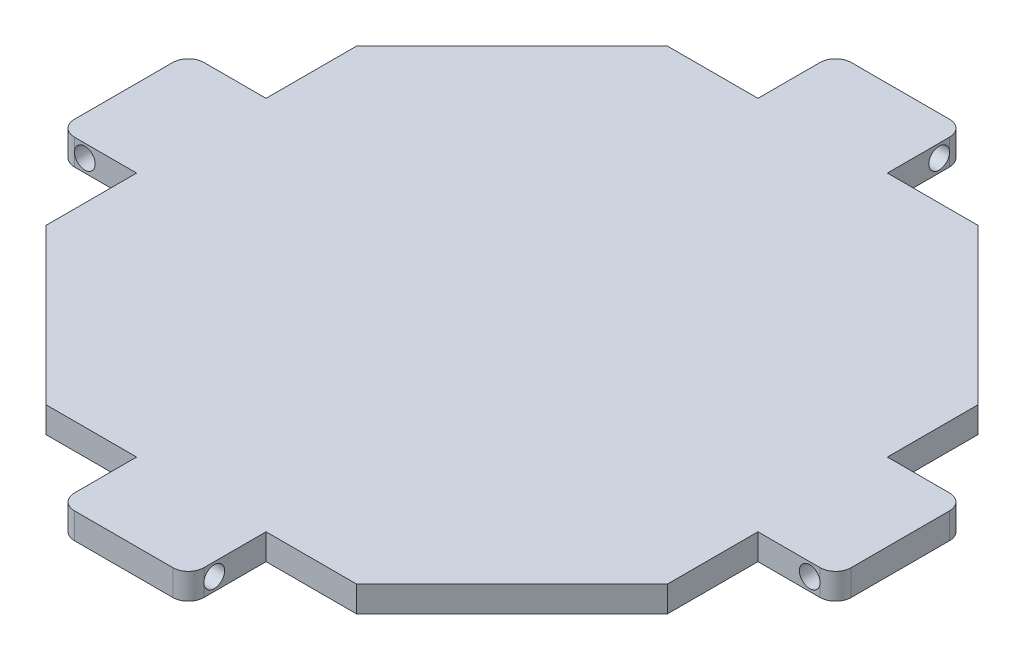
SolidWorks part; units mm, degrees
material "6061 합금"
ref_plane "정면" through (0, 0, 0) normal (0, 0, 1) x (1, 0, 0)
ref_plane "윗면" through (0, 0, 0) normal (0, 1, 0) x (1, 0, 0)
ref_plane "우측면" through (0, 0, 0) normal (1, 0, 0) x (0, 0, -1)
sketch "스케치1" plane through (0, 0, 0) normal (0, 1, 0) x (1, 0, 0)
  line L7 (39, 0) -> (-66.3, 0) construction
  line L9 (0, 39) -> (0, -39) construction
  line L14 (-30, -60) -> (30, -60)
  line L15 (30, -60) -> (60, -30)
  line L16 (60, -30) -> (60, 30)
  line L17 (60, 30) -> (30, 60)
  line L18 (30, 60) -> (-30, 60)
  line L19 (-30, 60) -> (-60, 30)
  line L20 (-60, 30) -> (-60, -30)
  line L21 (-60, -30) -> (-30, -60)
  line L22 (-60, 12.5) -> (-75, 12.5)
  line L23 (-75, 12.5) -> (-75, -12.5)
  line L24 (-75, -12.5) -> (-60, -12.5)
  line L25 (-12.5, -60) -> (-12.5, -75)
  line L26 (-12.5, -75) -> (12.5, -75)
  line L27 (12.5, -75) -> (12.5, -60)
  line L28 (60, -12.5) -> (75, -12.5)
  line L29 (75, -12.5) -> (75, 12.5)
  line L30 (75, 12.5) -> (60, 12.5)
  line L31 (-12.5, 60) -> (-12.5, 75)
  line L32 (-12.5, 75) -> (12.5, 75)
  line L33 (12.5, 75) -> (12.5, 60)
  point P0 (0, 0)
  dimension "D3" = 60
  dimension "D4" = 60
  dimension "D5" = 60
  dimension "D6" = 60
  dimension "D7" = 30
  dimension "D8" = 30
  dimension "D9" = 30
  dimension "D10" = 30
  dimension "D11" = 30
  dimension "D12" = 30
  dimension "D13" = 30
  dimension "D15" = 25
  dimension "D16" = 25
  dimension "D17" = 25
  dimension "D18" = 25
  dimension "D19" = 15
  dimension "D21" = 15
  dimension "D22" = 15
  dimension "D23" = 15
  dimension "D24" = 12.5
  dimension "D25" = 12.5
  dimension "D26" = 12.5
extrude "보스-돌출1" add sketch "스케치1" along normal blind 5
fillet "필렛1" radius 3 8 edges at (-12.5, 2.5, 75) (75, 2.5, 12.5) (75, 2.5, -12.5) (12.5, 2.5, -75) (-12.5, 2.5, -75) (-75, 2.5, -12.5) (-75, 2.5, 12.5) (12.5, 2.5, 75)
sketch "스케치11" plane through (0, 0, 12.5) normal (0, 0, 1) x (1, 0, 0)
  line L0 (-75, 0) -> (-75, 5) construction
  line L1 (-72, 5) -> (-60, 5) construction
  line L2 (75, 5) -> (75, 0) construction
  line L3 (60, 5) -> (72, 5) construction
  circle A0 centre (-70, 2.5) radius 2
  circle A1 centre (70, 2.5) radius 2
  dimension "D1" = 4
  dimension "D6" = 4
  dimension "D2" = 5
  dimension "D3" = 2.5
  dimension "D4" = 5
  dimension "D5" = 2.5
extrude "컷-돌출6" cut sketch "스케치11" against normal through all
sketch "스케치12" plane through (-12.5, 0, 0) normal (-1, 0, 0) x (0, 0, 1)
  line L0 (-75, 0) -> (-75, 5) construction
  line L1 (-60, 5) -> (-72, 5) construction
  line L2 (75, 5) -> (75, 0) construction
  circle A0 centre (-70, 2.5) radius 2
  circle A1 centre (70, 2.5) radius 2
  dimension "D3" = 4
  dimension "D4" = 4
  dimension "D1" = 5
  dimension "D2" = 2.5
  dimension "D5" = 5
extrude "컷-돌출7" cut sketch "스케치12" against normal through all
